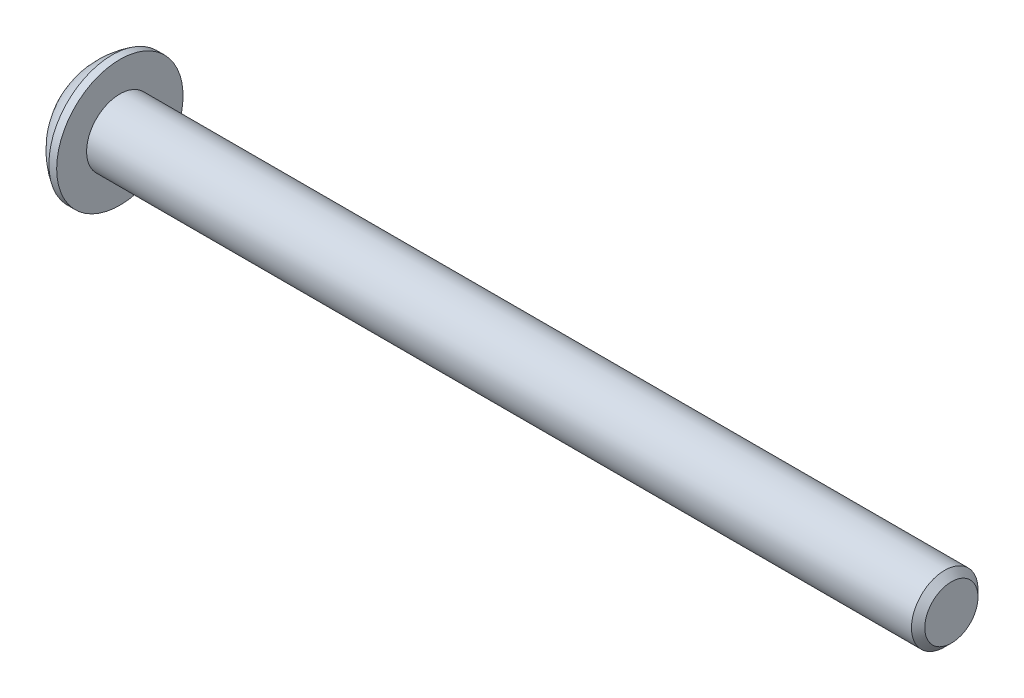
SolidWorks part; units mm, degrees
material "AISI 304"
ref_plane "Front Plane" through (0, 0, 0) normal (0, 0, 1) x (1, 0, 0)
ref_plane "Top Plane" through (0, 0, 0) normal (0, 1, 0) x (1, 0, 0)
ref_plane "Right Plane" through (0, 0, 0) normal (1, 0, 0) x (0, 0, -1)
sketch "Sketch2" plane through (0, 0, 0) normal (0, 0, 1) x (1, 0, 0)
  line L0 (0, 0) -> (39.15, 0)
  line L1 (39.15, 0) -> (39.15, 1.5)
  line L2 (39.15, 1.5) -> (1.65, 1.5)
  line L3 (1.65, 1.5) -> (1.65, 2.85)
  line L4 (0, 1.425) -> (0, 0)
  line L5 (1.65, 2.85) -> (1.3, 2.85)
  arc A1 (1.3, 2.85) -> (0, 1.425) centre (3.1356, -0.13) ccw
  point P9 (1.3, -0.65)
  point P10 (0, 0)
  point P11 (0, 1.7254)
  dimension "D1" = 37.5
  dimension "D3" = 2.85
  dimension "D6" = 3.5
  dimension "D7" = 1.425
  dimension "D2" = 1.5
  dimension "D4" = 0.35
  dimension "D5" = 1.65
revolve "Revolve1" add sketch "Sketch2" angle 360 about L0
chamfer "Chamfer1" distance 0.3 angle 45 1 edges at (39.15, 0, 1.5)
sketch "Sketch3" plane through (0, 0, 0) normal (-1, 0, 0) x (0, 0, 1)
  line L7 (0.576, 1.0008) -> (-0.5787, 0.9992)
  line L8 (-0.5787, 0.9992) -> (-1.1547, -0.0015)
  line L9 (-1.1547, -0.0015) -> (-0.576, -1.0008)
  line L10 (-0.576, -1.0008) -> (0.5787, -0.9992)
  line L11 (0.5787, -0.9992) -> (1.1547, 0.0015)
  line L12 (1.1547, 0.0015) -> (0.576, 1.0008)
  circle A0 centre (0, 0) radius 1 construction
  dimension "D2" = 1.0008
  dimension "D1" = 2
extrude "Cut-Extrude1" cut sketch "Sketch3" against normal blind 1
